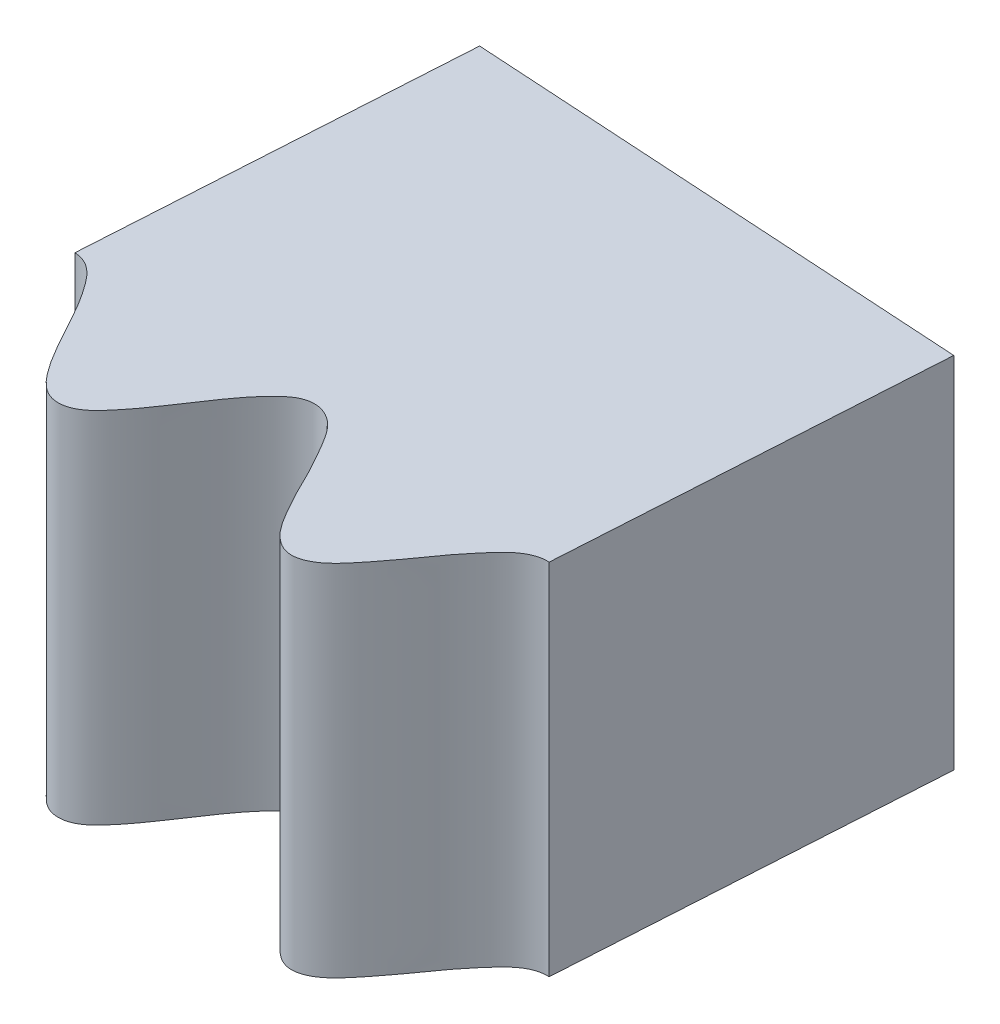
SolidWorks part; units mm, degrees
ref_plane "Front Plane" through (0, 0, 0) normal (0, 0, 1) x (1, 0, 0)
ref_plane "Top Plane" through (0, 0, 0) normal (0, 1, 0) x (1, 0, 0)
ref_plane "Right Plane" through (0, 0, 0) normal (1, 0, 0) x (0, 0, -1)
sketch "Sketch1" plane through (0, 0, 0) normal (0, 1, 0) x (1, 0, 0)
  line L0 (0, 80) -> (0, 85)
  line L1 (80, 0) -> (85, 0)
  arc A0 (0, 85) -> (85, 0) centre (0, 0) cw
  spline S0 degree 4 number of poles 785 (79.0126, -11.2218) -> (-11.2767, 79.3979) construction
  spline S1 degree 4 number of poles 659 (80, 0) -> (0, 80)
  dimension "D1" = 85
extrude "Boss-Extrude1" add sketch "Sketch1" along normal blind 4
sketch "Sketch3" plane through (0, 4, 0) normal (0, 1, 0) x (1, 0, 0)
  line L0 (2.1137, 80.7185) -> (2.3735, 84.9669)
  line L3 (0, 85) -> (0, 80) construction
  line L4 (0, 85) -> (0, 80)
  arc A1 (85, 0) -> (0, 85) centre (0, 0) ccw construction
  arc A3 (2.3735, 84.9669) -> (0, 85) centre (0, 0) ccw
  spline S0 degree 4 number of poles 659 (0, 80) -> (80, 0) construction
  dimension "D1" = 3.5
  dimension "D2" = 1.5
extrude "Cut-Extrude2" cut sketch "Sketch3" against normal through all both and the other way through all
sketch "Sketch2" plane through (0, 4, 0) normal (0, 1, 0) x (1, 0, 0)
  line L0 (7.999, 84.6228) -> (7.7392, 80.3749)
  line L1 (2.3735, 84.9669) -> (2.1137, 80.7185) construction
  arc A0 (85, 0) -> (2.3735, 84.9669) centre (0, 0) ccw construction
  arc A1 (85, 0) -> (7.999, 84.6228) centre (0, 0) ccw
  spline S1 degree 4 number of poles 648 (2.1137, 80.7185) -> (80, 0) construction
  dimension "D1" = 4
extrude "Cut-Extrude1" cut sketch "Sketch2" against normal through all both and the other way through all
sketch "Sketch4" plane through (0, 4, 0) normal (0, 1, 0) x (1, 0, 0)
  line L0 (2.3735, 84.9669) -> (7.999, 84.6228)
  arc A0 (7.999, 84.6228) -> (2.3735, 84.9669) centre (0, 0) ccw construction
  arc A1 (7.999, 84.6228) -> (2.3735, 84.9669) centre (0, 0) ccw
extrude "Cut-Extrude3" cut sketch "Sketch4" against normal through all both and the other way through all
ref_plane "Plane1" through (0, 0, 0) normal (0.9981, 0, 0.061) x (0.061, 0, -0.9981)
